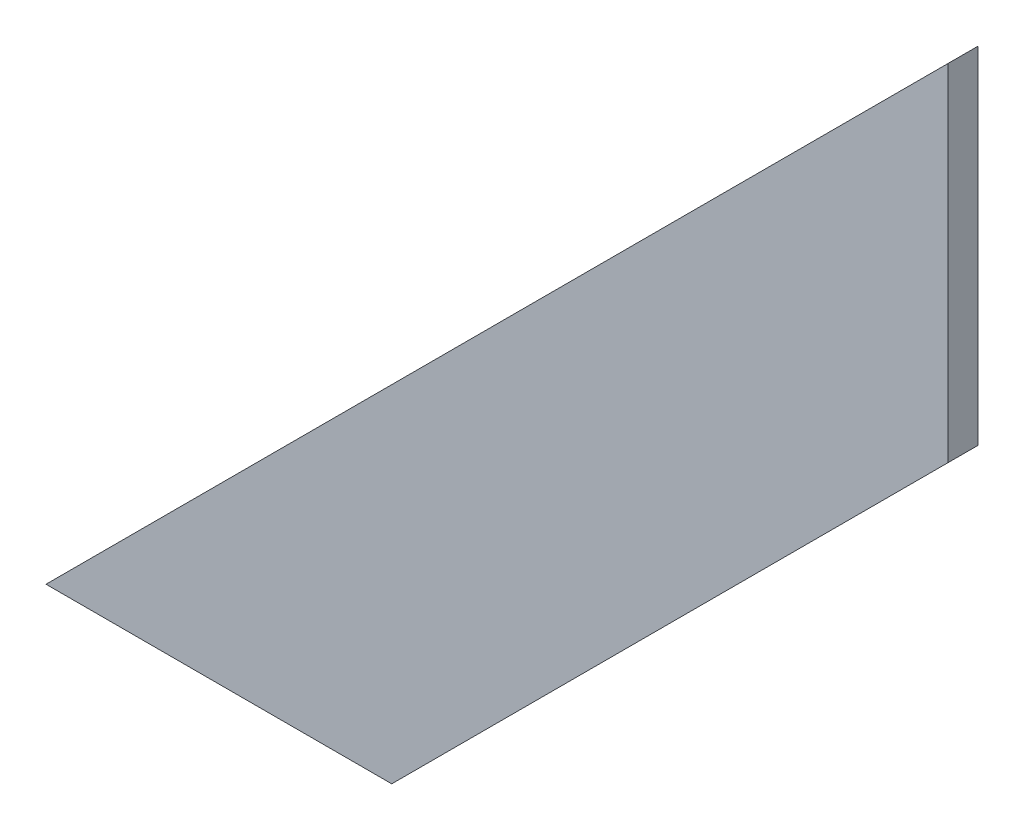
SolidWorks part; units mm, degrees
ref_plane "Front Plane" through (0, 0, 0) normal (0, 0, 1) x (1, 0, 0)
ref_plane "Top Plane" through (0, 0, 0) normal (0, 1, 0) x (1, 0, 0)
ref_plane "Right Plane" through (0, 0, 0) normal (1, 0, 0) x (0, 0, -1)
sketch "Sketch1" plane through (0, 0, 0) normal (0, 0, 1) x (1, 0, 0)
  line L0 (0, 0) -> (60, 60)
  line L1 (60, 60) -> (60, 37)
  line L2 (60, 37) -> (23, 0)
  line L3 (23, 0) -> (0, 0)
  dimension "D1" = 60
  dimension "D2" = 45
  dimension "D3" = 37
extrude "Boss-Extrude1" add sketch "Sketch1" along normal blind 2
